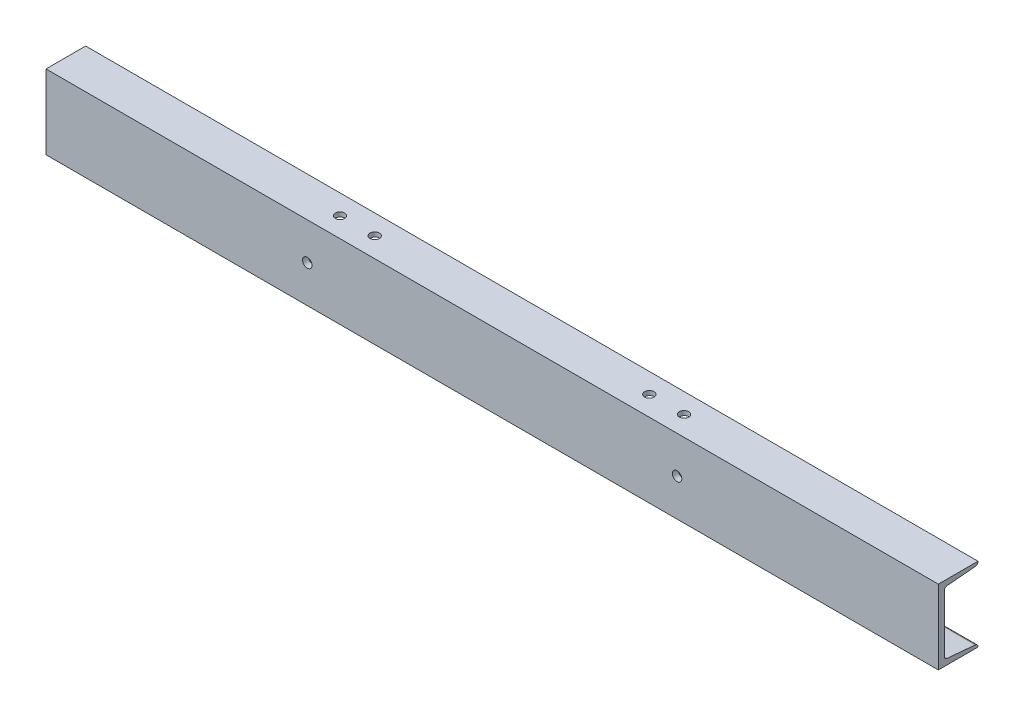
SolidWorks part; units mm, degrees
material "Plain Carbon Steel"
ref_plane "Front Plane" through (0, 0, 0) normal (0, 0, 1) x (1, 0, 0)
ref_plane "Top Plane" through (0, 0, 0) normal (0, 1, 0) x (1, 0, 0)
ref_plane "Right Plane" through (0, 0, 0) normal (1, 0, 0) x (0, 0, -1)
sketch "Sketch1" plane through (0, 0, 0) normal (0, 1, 0) x (1, 0, 0)
  line L0 (-450, 0) -> (450, 0)
  dimension "D1" = 900
other "Structural Member1"
ref_plane "Plane1" through (-450, 0, 0) normal (1, 0, 0) x (0, 0, 1)
sketch "Sketch19" plane through (-450, 0, 0) normal (1, 0, 0) x (0, 0, 1)
  line L0 (0, 37.5) -> (0, -37.5)
  line L1 (0, 37.5) -> (-40, 37.5)
  line L2 (0, -37.5) -> (-40, -37.5)
  line L3 (-6, 28.7531) -> (-6, -28.7531)
  line L4 (-8.7363, 31.7414) -> (-37.2637, 34.2586)
  line L5 (0, 0) -> (-48.9646, 0) construction
  line L6 (-40, 37.2469) -> (-40, 37.5)
  line L7 (-8.7363, -31.7414) -> (-37.2637, -34.2586)
  line L8 (-40, -37.2469) -> (-40, -37.5)
  arc A0 (-6, 28.7531) -> (-8.7363, 31.7414) centre (-9, 28.7531) ccw
  arc A1 (-37.2637, 34.2586) -> (-40, 37.2469) centre (-37, 37.2469) cw
  arc A2 (-6, -28.7531) -> (-8.7363, -31.7414) centre (-9, -28.7531) cw
  arc A3 (-37.2637, -34.2586) -> (-40, -37.2469) centre (-37, -37.2469) ccw
  point P6 (0, 0)
  point P12 (-6, 31.5)
  point P15 (-40, 34.5)
  dimension "D6" = 3
  dimension "D1" = 75
  dimension "D2" = 40
  dimension "D3" = 6
  dimension "D4" = 3
  dimension "D5" = 6
sketch "Sketch12" plane through (0, 0, 0) normal (0, 1, 0) x (1, 0, 0)
  line L0 (-412.5239, 20) -> (413.742, 20) construction
  line L1 (-450, 0) -> (450, 0) construction
  line L2 (0, 0) -> (0, 45.9021) construction
  line L4 (-450, 40) -> (-450, 0) construction
  circle A0 centre (-425, 20) radius 4.7625
  circle A1 centre (425, 20) radius 4.7625
  dimension "D2" = 9.525
  dimension "D1" = 20
  dimension "D3" = 25
extrude "Cut-Extrude1" cut sketch "Sketch12" against normal through all
sketch "Sketch15" plane through (0, 0, -6) normal (0, 0, -1) x (-1, 0, 0)
  line L0 (-425, 105.8991) -> (-425, -40.4286) construction
  line L1 (-375.1366, 27.5) -> (-474.8634, 27.5) construction
  line L3 (-412.5, 27.5) -> (-437.5, 27.5) construction
  line L4 (-412.5, 22.5) -> (-437.5, 22.5)
  line L5 (-412.5, 32.5) -> (-437.5, 32.5)
  line L6 (0, 0) -> (0, -58.1771) construction
  line L7 (412.5, 27.5) -> (437.5, 27.5) construction
  line L8 (412.5, 22.5) -> (437.5, 22.5)
  line L9 (412.5, 32.5) -> (437.5, 32.5)
  line L10 (-450, 37.5) -> (450, 37.5) construction
  arc A0 (-412.5, 22.5) -> (-412.5, 32.5) centre (-412.5, 27.5) ccw
  arc A1 (-437.5, 32.5) -> (-437.5, 22.5) centre (-437.5, 27.5) ccw
  arc A2 (412.5, 22.5) -> (412.5, 32.5) centre (412.5, 27.5) cw
  arc A3 (437.5, 32.5) -> (437.5, 22.5) centre (437.5, 27.5) cw
  ellipse E0 centre (-425, 32.7353) end of major axis (-429.7625, 32.7353) minor radius 0.4202 construction
  point P0 (-425, 32.7353)
  point P11 (-425, 27.5)
  point P16 (-425, 27.5)
  point P26 (425, 27.5)
  dimension "D2" = 5
  dimension "D1" = 10
  dimension "D3" = 25
extrude "Cut-Extrude2" cut sketch "Sketch15" along normal blind 40
sketch "Sketch16" plane through (0, 0, 0) normal (0, 1, 0) x (1, 0, 0)
  line L0 (0, -46.4014) -> (0, 86.4014) construction
  line L1 (-394.0256, 20) -> (394.0256, 20) construction
  line L3 (450, 0) -> (-450, 0) construction
  circle A0 centre (-173.5, 20) radius 4.7625
  circle A1 centre (-138.5, 20) radius 4.7625
  circle A2 centre (138.5, 20) radius 4.7625
  circle A3 centre (173.5, 20) radius 4.7625
  point P5 (0, 20)
  point P6 (0, 20)
  dimension "D2" = 9.525
  dimension "D1" = 20
  dimension "D3" = 173.5
  dimension "D4" = 35
extrude "Cut-Extrude3" cut sketch "Sketch16" along normal through all
sketch "Sketch17" plane through (0, 0, 0) normal (0, 0, 1) x (1, 0, 0)
  line L0 (0, 0) -> (0, 84.0393) construction
  line L1 (0, 0) -> (-474.9461, 0) construction
  circle A0 centre (-186.5, 0) radius 4.7625
  circle A1 centre (186.5, 0) radius 4.7625
  dimension "D1" = 9.525
  dimension "D2" = 186.5
extrude "Cut-Extrude4" cut sketch "Sketch17" against normal through all
